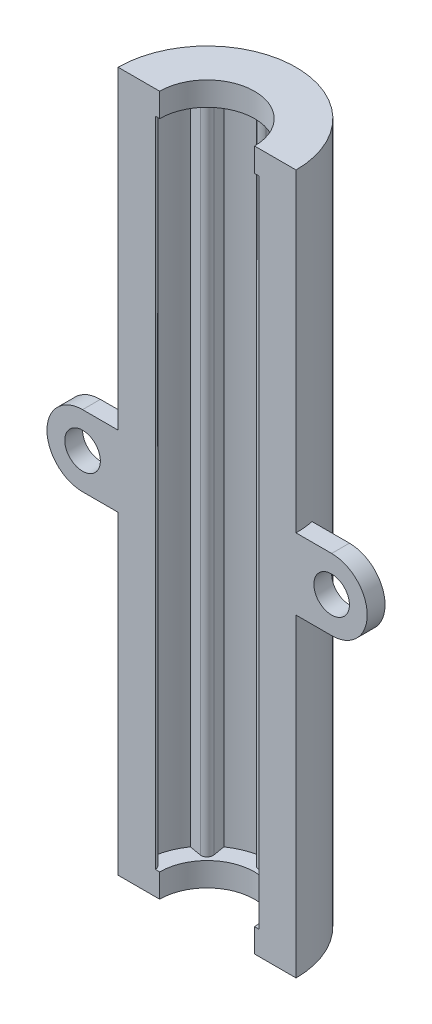
SolidWorks part; units mm, degrees
ref_plane "Front" through (0, 0, 0) normal (0, 0, 1) x (1, 0, 0)
ref_plane "Top" through (0, 0, 0) normal (0, 1, 0) x (1, 0, 0)
ref_plane "Right" through (0, 0, 0) normal (1, 0, 0) x (0, 0, -1)
sketch "Sketch1" plane through (0, 0, 0) normal (0, 1, 0) x (1, 0, 0)
  circle A0 centre (0, 0) radius 7.5
  dimension "D1" = 15
extrude "Boss-Extrude1" add sketch "Sketch1" along normal blind 55
sketch "Sketch3" plane through (0, 55, 0) normal (0, 1, 0) x (1, 0, 0)
  line L0 (-1, 5.4083) -> (-0.4077, 4.5741)
  line L1 (0.4077, 4.5741) -> (1, 5.4083)
  line L2 (3.5227, 2.9461) -> (4.5314, 3.1172)
  line L3 (3.1172, 4.5314) -> (2.9461, 3.5227)
  line L4 (4.5741, -0.4077) -> (5.4083, -1)
  line L5 (5.4083, 1) -> (4.5741, 0.4077)
  line L6 (2.9461, -3.5227) -> (3.1172, -4.5314)
  line L7 (4.5314, -3.1172) -> (3.5227, -2.9461)
  line L8 (-0.4077, -4.5741) -> (-1, -5.4083)
  line L9 (1, -5.4083) -> (0.4077, -4.5741)
  line L10 (-3.5227, -2.9461) -> (-4.5314, -3.1172)
  line L11 (-3.1172, -4.5314) -> (-2.9461, -3.5227)
  line L12 (-4.5741, 0.4077) -> (-5.4083, 1)
  line L13 (-5.4083, -1) -> (-4.5741, -0.4077)
  line L14 (-2.9461, 3.5227) -> (-3.1172, 4.5314)
  line L15 (-4.5314, 3.1172) -> (-3.5227, 2.9461)
  circle A0 centre (0, 0) radius 5.5
  circle A1 centre (0, 0) radius 7.5 construction
  arc A2 (-0.4077, 4.5741) -> (0.4077, 4.5741) centre (0, 4.8636) ccw
  arc A3 (2.9461, 3.5227) -> (3.5227, 2.9461) centre (3.4391, 3.4391) ccw
  arc A4 (4.5741, 0.4077) -> (4.5741, -0.4077) centre (4.8636, 0) ccw
  arc A5 (3.5227, -2.9461) -> (2.9461, -3.5227) centre (3.4391, -3.4391) ccw
  arc A6 (0.4077, -4.5741) -> (-0.4077, -4.5741) centre (0, -4.8636) ccw
  arc A7 (-2.9461, -3.5227) -> (-3.5227, -2.9461) centre (-3.4391, -3.4391) ccw
  arc A8 (-4.5741, -0.4077) -> (-4.5741, 0.4077) centre (-4.8636, 0) ccw
  arc A9 (-3.5227, 2.9461) -> (-2.9461, 3.5227) centre (-3.4391, 3.4391) ccw
  point P12 (0, 4)
  point P48 (0, 0)
  dimension "D1" = 2
  dimension "D4" = 0.5
  dimension "D2" = 4
  dimension "D3" = 2
  dimension "D5" = 8
extrude "Cut-Extrude2" cut sketch "Sketch3" against normal through all contours A9 L15 A0 L12 A8 L13 L10 A7 L11 L8 A6 L9 L6 A5 L7 L4 A4 L5 L2 A3 L3 L1 A2 L0 L14
sketch "Sketch4" plane through (0, 0, 0) normal (0, 1, 0) x (1, 0, 0)
  circle A1 centre (0, 0) radius 4
  circle A2 centre (0, 0) radius 7.5 construction
  circle A3 centre (0, 0) radius 7.5
  dimension "D1" = 8
extrude "Boss-Extrude2" add sketch "Sketch4" against normal blind 2 contours A1 | A3
pattern_linear "LPattern1" count 2 spacing 57 along (0, 1, 0) of "Boss-Extrude2"
sketch "Sketch6" plane through (0, 0, 0) normal (0, 0, 1) x (1, 0, 0)
  line L0 (7.5, -2) -> (7.5, 57) construction
  line L1 (-13.5, 30.5) -> (13.5, 30.5)
  line L2 (-13.5, 30.5) -> (-13.5, 24.5)
  line L3 (-13.5, 24.5) -> (13.5, 24.5)
  line L4 (13.5, 30.5) -> (13.5, 24.5)
  line L5 (-13.5, 30.5) -> (13.5, 24.5) construction
  line L6 (-13.5, 24.5) -> (13.5, 30.5) construction
  line L7 (7.5, -2) -> (7.5, 57) construction
  line L8 (-6, 30.5) -> (-6, 24.5)
  line L9 (6, 30.5) -> (6, 24.5)
  circle A0 centre (-10.5, 27.5) radius 3
  circle A1 centre (10.5, 27.5) radius 3
  circle A2 centre (-10.5, 27.5) radius 1.5
  circle A3 centre (10.5, 27.5) radius 1.5
  point P0 (0, 27.5)
  point P8 (7.5, 27.5)
  dimension "D3" = 3
  dimension "D1" = 6
  dimension "D2" = 6
  dimension "D4" = 12
  dimension "D5" = 6
extrude "Boss-Extrude3" add sketch "Sketch6" along normal mid plane 3 contours A0 L3 L8 L1 | A1 L1 L9 L3 | A1 A3 | A0 A2
sketch "Sketch7" plane through (0, 0, 0) normal (0, 1, 0) x (1, 0, 0)
  line L0 (-13.5, 1.5) -> (-13.5, -1.5) construction
  line L1 (-13.5, 0) -> (13.5, 0)
  line L2 (-13.5, 0) -> (-13.5, -7.5)
  line L3 (-13.5, -7.5) -> (13.5, -7.5)
  line L4 (13.5, 0) -> (13.5, -7.5)
  circle A0 centre (0, 0) radius 7.5 construction
  point P4 (0, 0)
extrude "Cut-Extrude3" cut sketch "Sketch7" against normal through all both and the other way through all
equation "\"D5@Sketch6\"=12.00mm/2"
